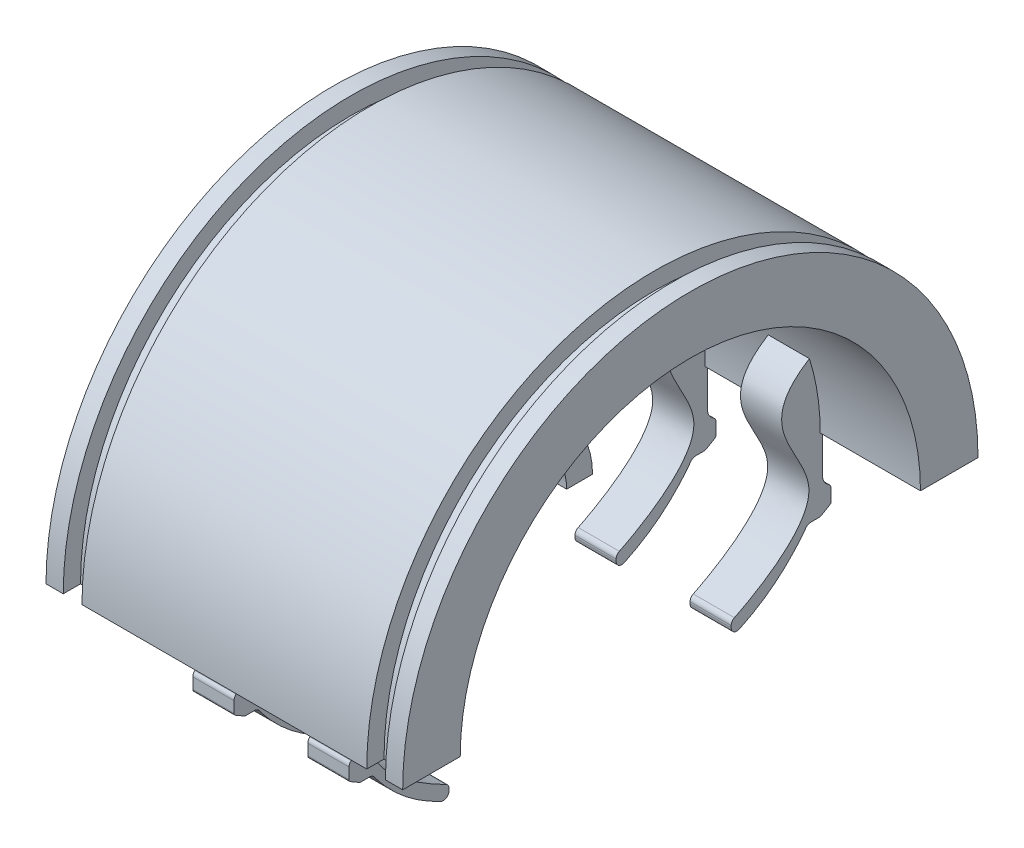
SolidWorks part; units mm, degrees
ref_plane "Front Plane" through (0, 0, 0) normal (0, 0, 1) x (1, 0, 0)
ref_plane "Top Plane" through (0, 0, 0) normal (0, 1, 0) x (1, 0, 0)
ref_plane "Right Plane" through (0, 0, 0) normal (1, 0, 0) x (0, 0, -1)
sketch "Sketch1" plane through (0, 0, 0) normal (0, 1, 0) x (1, 0, 0)
  line L0 (0, 0) -> (155.1991, 0) construction
  line L1 (155.1991, 0) -> (-158.5278, 0) construction
  line L2 (0, 0) -> (0, -90.4212) construction
  line L3 (0, 0) -> (0, 195.4795) construction
  line L9 (24.75, 47) -> (28, 47)
  line L10 (31, 50) -> (28, 50)
  line L15 (31, 50) -> (31, 40)
  line L16 (31, 40) -> (-26, 40)
  line L22 (-31, 50) -> (-31, 40)
  line L23 (31, 50) -> (28, 49.5161) construction
  line L24 (31, 40) -> (-24.75, 48.9919) construction
  line L26 (-24.75, 50) -> (-24.75, 47)
  line L27 (-24.75, 47) -> (-28, 47)
  line L28 (-28, 50) -> (-28, 47)
  line L29 (24.75, 50) -> (-24.75, 50)
  line L30 (24.75, 48.9919) -> (-26, 40.8065) construction
  line L35 (28, 50) -> (28, 47)
  line L36 (24.75, 50) -> (24.75, 47)
  line L38 (-28, 50) -> (-31, 50)
  line L39 (-28, 49.5161) -> (-31, 50) construction
  line L40 (-26, 77.8545) -> (-26, 16.5) construction
  line L41 (-35, 76.0219) -> (-35, -31.7141) construction
  line L42 (-31, 40) -> (-31, -27.11) construction
  line L43 (-97.0302, 16.5) -> (67.6651, 16.5) construction
  line L44 (-97.0302, 14) -> (77.1364, 14) construction
  line L45 (-85.0595, 9.5) -> (85.95, 9.5) construction
  line L46 (-80.3239, 27.25) -> (68.7175, 27.25) construction
  line L47 (-10, 63.6566) -> (-10, -23.2952) construction
  line L48 (-28, 68.9882) -> (-28, -37.4297) construction
  line L49 (-24.75, 67.96) -> (-24.75, -40.5143) construction
  line L50 (-18.153, 23.85) -> (-54.2967, 23.85) construction
  line L51 (-18.153, 18.7) -> (-49.456, 18.7) construction
  line L52 (-9.9469, 14) -> (-10, 9.5)
  spline S0 degree 3 poles (-31, 40) (-32.9396, 37.5406) (-36.9339, 27.5823) (-30.0824, 11.7757) (-17.9219, 9.5) (-10, 9.5) knots 0 0 0 0 0.268185 0.444495 0.82256 0.82256 0.82256 0.82256
  spline S1 degree 3 poles (-26, 40) (-27.0137, 36.8092) (-29.3451, 27.8281) (-24.5235, 15.3947) (-15.5263, 14.8685) (-9.9469, 14) knots 0 0 0 0 0.285239 0.456571 0.779818 0.779818 0.779818 0.779818
  point P3 (0, 45)
  point P11 (-26.375, 50)
  dimension "D14" = 3
  dimension "D1" = 62
  dimension "D2" = 10
  dimension "D3" = 50
  dimension "D4" = 3
  dimension "D5" = 3
  dimension "D6" = 5
  dimension "D7" = 4
  dimension "D8" = 23.5
  dimension "D9" = 26
  dimension "D10" = 30.5
  dimension "D11" = 12.75
  dimension "D12" = 21
  dimension "D13" = 10
  dimension "D15" = 6.25
  dimension "D16" = 16.15
  dimension "D17" = 21.3
revolve "Revolve1" add sketch "Sketch1" angle 180 about L0
ref_plane "Plane1" through (0, 0, 0) normal (0, -1, 0) x (-1, 0, 0)
sketch "Sketch2" plane through (0, 0, 0) normal (0, -1, 0) x (-1, 0, 0)
  line L0 (0, 0) -> (0, -63.4772) construction
  line L1 (0, -63.4772) -> (0, 65.8935) construction
  line L2 (0, 0) -> (-92.8791, 0) construction
  line L3 (-92.8791, 0) -> (91.2198, 0) construction
  line L4 (-11.5, -45) -> (11.5, -45) construction
  line L17 (-20, -43.62) -> (-20, -63.3325) construction
  line L18 (-22.3, -45) -> (37.0527, -45) construction
  line L19 (-31, -45) -> (51.3033, -45) construction
  line L20 (-31, -40) -> (-31, -50) construction
  line L22 (31, -50) -> (31, 49950) construction
  line L23 (-31, -50) -> (-31, 49950) construction
  line L25 (31, -50) -> (50031, -50) construction
  line L26 (-31, -40) -> (-50031, -40) construction
  line L27 (20, -62.5861) -> (20, 49937.4139) construction
  line L28 (0, 27.5) -> (0, -27.5) construction
  circle A0 centre (0, -45) radius 3.9128
  circle A1 centre (19.9915, -45) radius 2.8027
  circle A2 centre (-19.9915, -45) radius 2.8027
  dimension "D2" = 7.8255
  dimension "D3" = 5.6055
  dimension "D1" = 20
  dimension "D7" = 20
sketch "Sketch6" plane through (0, 0, 0) normal (1, 0, 0) x (0, 0, -1)
  line L0 (-29.6412, 0) -> (65.6482, 0) construction
  line L1 (37.3637, 0) -> (-37.3637, 0) construction
  line L2 (-14, 0) -> (-9.5, 0)
  line L3 (9.5, 0) -> (14, 0)
  arc A0 (9.5, 0) -> (-9.5, 0) centre (0, 0) ccw
  arc A1 (14, 0) -> (-14, 0) centre (0, 0) ccw
extrude "Boss-Extrude1" add sketch "Sketch6" against normal up to surface (31 mm away) up to face at (-31, 22.5, 0)
ref_plane "Plane3" through (31, 0, 0) normal (1, 0, 0) x (0, 0, -1)
sketch "Sketch7" plane through (31, 0, 0) normal (1, 0, 0) x (0, 0, -1)
  line L0 (4.7883, 13.1557) -> (13.6808, 37.5877)
  line L1 (-4.7883, 13.1557) -> (-13.6808, 37.5877)
  line L2 (0, 27.5) -> (0, -27.5) construction
  arc A0 (4.7883, 13.1557) -> (-4.7883, 13.1557) centre (0, 0) ccw
  arc A1 (13.6808, 37.5877) -> (-13.6808, 37.5877) centre (0, 0) ccw
  dimension "D1" = 20
  dimension "D2" = 20
extrude "Cut-Extrude2" cut sketch "Sketch7" against normal blind 74
pattern_circular "CirPattern2" count 6 over 360 about axis through (0, 0, 0) along (1, 0, 0) of "Cut-Extrude2"
extrude "Cut-Extrude4" cut sketch "Sketch2" against normal blind 8.72
mirror "Mirror1" about plane through (0, 0, 0) normal (0, 0, 1) of "Cut-Extrude4"
ref_plane "Plane4" through (10, 0, 0) normal (1, 0, 0) x (0, 0, -1)
ref_plane "Plane5" through (-10, 0, 0) normal (1, 0, 0) x (0, 0, -1)
ref_plane "Plane6" through (10, 0, 0) normal (1, 0, 0) x (0, 0, -1)
sketch "Sketch13" plane through (10, 0, 0) normal (1, 0, 0) x (0, 0, -1)
  line L0 (-50, 0) -> (-50, 50000) construction
  line L1 (0, 27.5) -> (0, -27.5) construction
  line L2 (-40, -1036.277) -> (-40, -7.6) construction
  line L3 (-22.0847, 10) -> (-68.0558, 10) construction
  line L4 (-45, -9.9894) -> (-45, 49990.0106) construction
  line L5 (-20.746, -23.597) -> (-50020.746, -23.597) construction
  line L6 (-2.2098, -17.5704) -> (-50002.2098, -17.5704) construction
  line L7 (-54.3944, 0) -> (49945.6056, 0) construction
  line L8 (-40.405, -7.6) -> (-40, -7.6)
  line L12 (-40, 0) -> (-37.229, 11.56) construction
  line L13 (-40, 0) -> (-40.405, 0)
  line L14 (-40, 0) -> (-40, 10) construction
  line L15 (-40, -12.6135) -> (-37.8234, -12.6135)
  line L16 (-41.905, -11.5136) -> (-41.905, -8.8586)
  line L19 (-41.5298, -11.7303) -> (-40, -7.6) construction
  line L20 (-40, -7.6) -> (-37.8234, -12.6135) construction
  line L21 (-40.405, 0) -> (-40.405, -7.6)
  line L22 (-40.405, -7.6) -> (-41.905, -8.8586)
  line L23 (-24.5204, -23.1135) -> (-24.5204, -20.6135)
  line L24 (-37.8234, -1012.2153) -> (-37.8234, -12.6135) construction
  line L25 (-35, -15.1457) -> (-35, 10) construction
  line L26 (-37.8234, -6.0719) -> (-37.8234, 11.9587) construction
  line L27 (-40, -12.6135) -> (-41.905, -11.5136)
  arc A0 (-38.1128, 12.1415) -> (-40, 0) centre (0, 0) ccw
  spline S0 degree 3 poles (-38.1128, 12.1415) (-27.1763, 5.3589) (-48.4004, -7.8358) (-28.1307, -18.9112) (-24.5204, -20.6135) knots 0 0 0 0 0.525362 1 1 1 1
  spline S1 degree 2 poles (-24.5204, -23.1135) (-32.7341, -19.7176) (-37.8234, -12.6135) knots 0 0 0 1 1 1
  point P23 (-38.0245, -7.6)
  point P41 (0, 0)
  point P42 (0, 0)
  dimension "D1" = 5
  dimension "D2" = 10
  dimension "D3" = 40
  dimension "D4" = 7.6
  dimension "D5" = 4.595
  dimension "D6" = 40
  dimension "D7" = 1.5
  dimension "D8" = 2.5
  dimension "D9" = 8
  dimension "D10" = 10
  dimension "D11" = 5
  dimension "D12" = 2.5
  dimension "D13" = 2.655
  dimension "D14" = 30
  dimension "D15" = 3
extrude "Boss-Extrude4" add sketch "Sketch13" along normal mid plane 7.155 contours L22 L16 L27 L15 S1 L23 S0 A0 L13 L21
mirror "Mirror5" about plane through (0, 0, 0) normal (1, 0, 0) of "Boss-Extrude4"
mirror "Mirror6" about plane through (0, 0, 0) normal (0, 0, 1) of "Boss-Extrude4", "Mirror5"
fillet "Fillet7" radius 1 8 edges at (-10, -20.6135, -24.5204) (-10, -23.1135, -24.5204) (10, -20.6135, -24.5204) (10, -23.1135, -24.5204) (-10, -23.1135, 24.5204) (-10, -20.6135, 24.5204) (10, -23.1135, 24.5204) (10, -20.6135, 24.5204)
fillet "Fillet8" radius 2 4 edges at (-10, -7.6, -40.405) (10, -7.6, -40.405) (-10, -7.6, 40.405) (10, -7.6, 40.405)
fillet "Fillet9" radius 1 4 edges at (-10, -8.8586, 41.905) (10, -8.8586, 41.905) (-10, -8.8586, -41.905) (10, -8.8586, -41.905)
fillet "Fillet10" radius 1 4 edges at (10, -12.6135, -37.8234) (-10, -12.6135, -37.8234) (-10, -12.6135, 37.8234) (10, -12.6135, 37.8234)
fillet "Fillet11" radius 0.5 8 edges at (10, -12.6135, -40) (-10, -11.5136, -41.905) (10, -11.5136, -41.905) (-10, -12.6135, -40) (-10, -12.6135, 40) (-10, -11.5136, 41.905) (10, -11.5136, 41.905) (10, -12.6135, 40)
